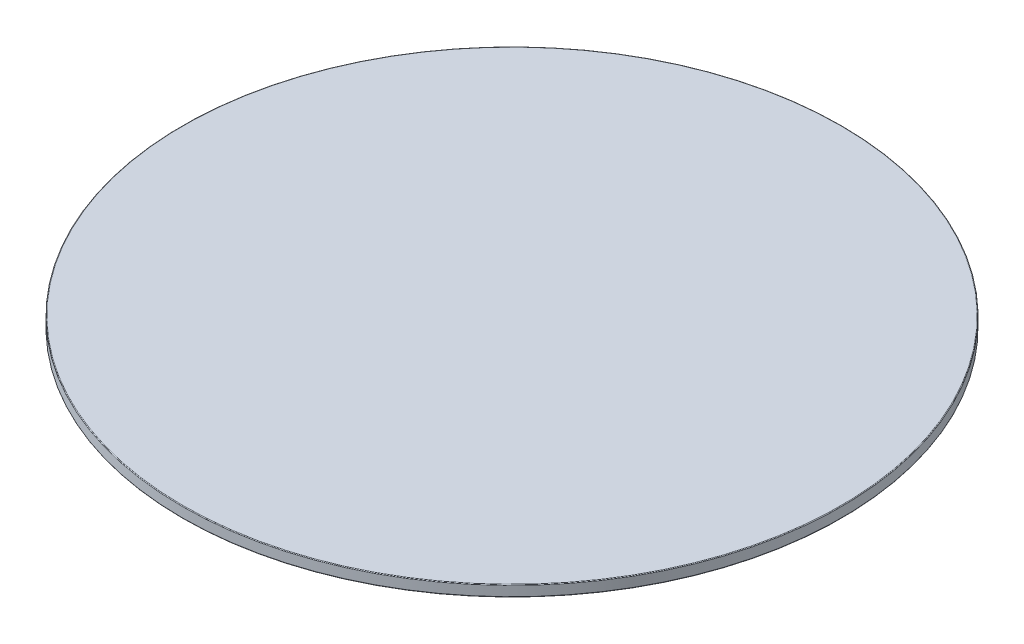
SolidWorks part; units mm, degrees
ref_plane "Front Plane" through (0, 0, 0) normal (0, 0, 1) x (1, 0, 0)
ref_plane "Top Plane" through (0, 0, 0) normal (0, 1, 0) x (1, 0, 0)
ref_plane "Right Plane" through (0, 0, 0) normal (1, 0, 0) x (0, 0, -1)
sketch "Sketch1" plane through (0, 0, 0) normal (0, 1, 0) x (1, 0, 0)
  circle A0 centre (0, 0) radius 150
  dimension "D1" = 300
extrude "Boss-Extrude1" add sketch "Sketch1" against normal blind 5
fillet "Fillet1" radius 0.3 2 edges at (0, 0, 150) (0, -5, 150)
equation "\"GlassPlateDiameter\"=300"
equation "\"D1@Sketch1\"=\"GlassPlateDiameter\""
